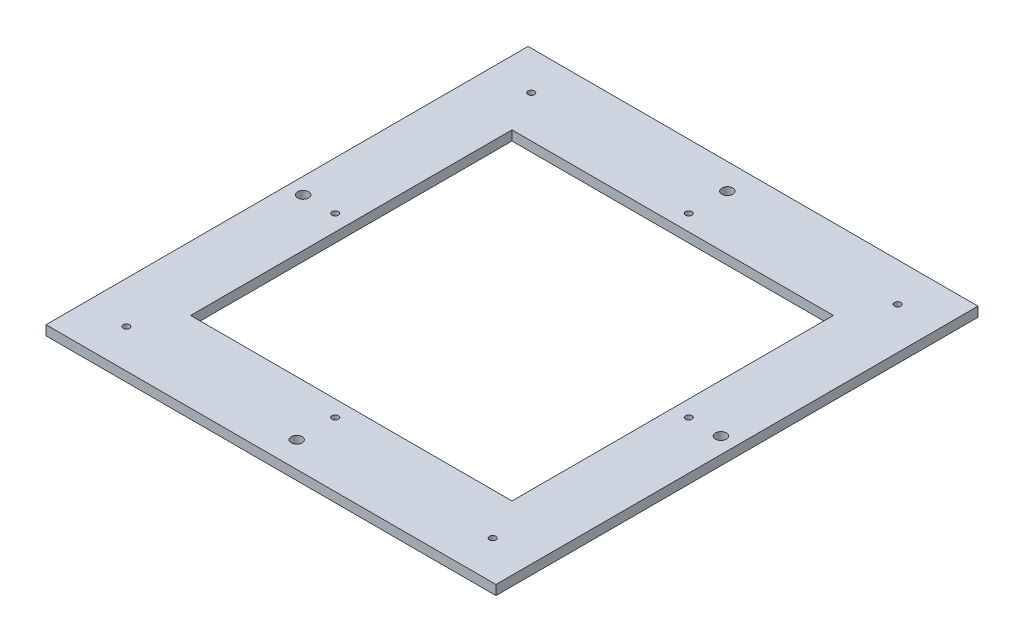
SolidWorks part; units mm, degrees
material "6061 合金"
ref_plane "前视基准面" through (0, 0, 0) normal (0, 0, 1) x (1, 0, 0)
ref_plane "上视基准面" through (0, 0, 0) normal (0, 1, 0) x (1, 0, 0)
ref_plane "右视基准面" through (0, 0, 0) normal (1, 0, 0) x (0, 0, -1)
sketch "草图1" plane through (0, 0, 0) normal (0, 0, 1) x (1, 0, 0)
  line L0 (12, 227.058) -> (152, 227.058)
  line L1 (12, 452.058) -> (12, 0) construction
  line L2 (152, 452.058) -> (152, 164.058) construction
  line L3 (152, 227.058) -> (12, 227.058) construction
extrude "拉伸-薄壁1" add sketch "草图1" along normal up to surface (150 mm away) thin contours L0
sketch "草图2" plane through (0, 224.058, 0) normal (0, -1, 0) x (1, 0, 0)
  line L1 (32, 125) -> (132, 125)
  line L2 (32, 125) -> (32, 25)
  line L3 (32, 25) -> (132, 25)
  line L4 (132, 125) -> (132, 25)
  line L5 (32, 125) -> (132, 25) construction
  line L6 (32, 25) -> (132, 125) construction
  point P0 (82, 75)
  point P2 (82, 75)
  dimension "D1" = 100
  dimension "D2" = 100
extrude "切除-拉伸1" cut sketch "草图2" against normal up to next
sketch "草图3" plane through (0, 224.058, 0) normal (0, -1, 0) x (1, 0, 0)
  line L3 (82, 75) -> (82, 142) construction
  line L10 (152, 150) -> (12, 150) construction
  line L11 (82, 75) -> (147, 75) construction
  line L12 (82, 75) -> (82, 8) construction
  line L13 (82, 75) -> (17, 75) construction
  line L14 (152, 150) -> (152, 0) construction
  line L15 (25, 150) -> (25, 0) construction
  line L16 (139, 150) -> (139, 0) construction
  line L17 (25, 150) -> (25, 0)
  line L18 (139, 150) -> (139, 0)
  line L27 (152, 150) -> (12, 150) construction
  line L28 (22, 135) -> (142, 135) construction
  line L29 (22, 135) -> (22, 15) construction
  line L30 (22, 15) -> (142, 15) construction
  line L31 (137, 20) -> (137, 130)
  line L32 (137, 130) -> (27, 130)
  line L33 (27, 130) -> (27, 20)
  line L34 (27, 20) -> (137, 20)
  line L35 (137, 20) -> (137, 130) construction
  line L36 (137, 130) -> (27, 130) construction
  line L37 (27, 130) -> (27, 20) construction
  line L38 (27, 20) -> (137, 20) construction
  line L39 (142, 135) -> (142, 15) construction
  line L40 (22, 135) -> (142, 15) construction
  line L41 (22, 15) -> (142, 135) construction
  line L42 (12, 0) -> (152, 0) construction
  point P1 (82, 20)
  point P7 (82, 130)
  point P11 (27, 75)
  point P12 (137, 75)
  point P22 (0, 0)
  point P23 (0, 0)
  point P24 (139, 12)
  point P25 (0, 0)
  point P26 (25, 12)
  point P30 (25, 138)
  point P34 (139, 138)
  point P40 (0, 0)
  point P41 (0, 0)
  point P42 (0, 0)
  point P43 (0, 0)
  point P44 (0, 0)
  point P49 (0, 0)
  point P52 (0, 0)
  point P53 (0, 0)
  point P54 (0, 0)
  point P55 (0, 0)
  point P56 (0, 0)
  point P57 (0, 0)
  point P58 (0, 0)
  point P59 (0, 0)
  point P60 (0, 0)
  point P61 (0, 0)
  point P62 (0, 0)
  point P63 (0, 0)
  point P64 (0, 0)
  point P65 (0, 0)
  point P66 (0, 0)
  point P67 (0, 0)
  dimension "D3" = 120
  dimension "D1" = 5
  dimension "D2" = 120
  dimension "D4" = 8
  dimension "D5" = 5
  dimension "D6" = 12
  dimension "D7" = 12
hole_wizard "M3 间隙孔1" positions "草图6" profile "草图7" hole size "M3" standard "GB" end condition through all
sketch "草图6" plane through (0, 224.058, 0) normal (0, -1, 0) x (-1, 0, 0)
  point P0 (-82, -142)
  point P3 (-147, -75)
  point P6 (-82, -8)
  point P9 (-17, -75)
sketch "草图7" plane through (82, 224.058, 142) normal (1, 0, 0) x (0, 0, -1)
  line L0 (0, 0) -> (0, 3)
  line L1 (0, 3) -> (1.7, 3)
  line L2 (1.7, 3) -> (1.7, 0)
  line L5 (1.7, 0) -> (0, 0)
  line L11 (0, -6.35) -> (0, 107.95) construction
  dimension "通孔孔直径" = 3.4
  dimension "通孔孔深度" = 3
hole_wizard "M3 螺纹孔的螺纹孔钻头1" positions "草图10" profile "草图11" hole size "M3" standard "GB" end condition through all
sketch "草图10" plane through (0, 224.058, 0) normal (0, -1, 0) x (-1, 0, 0)
  point P0 (-139, -138)
  point P3 (-25, -138)
  point P6 (-82, -130)
  point P9 (-27, -75)
  point P12 (-137, -75)
  point P15 (-82, -20)
  point P18 (-25, -12)
  point P21 (-139, -12)
sketch "草图11" plane through (139, 224.058, 138) normal (1, 0, 0) x (0, 0, -1)
  line L0 (0, 0) -> (0, 3)
  line L1 (0, 3) -> (1, 3)
  line L2 (1, 3) -> (1, 0)
  line L5 (1, 0) -> (0, 0)
  line L11 (0, -6.35) -> (0, 107.95) construction
  dimension "通孔孔直径" = 2
  dimension "通孔孔深度" = 3
equation "\"D2@草图2\"=\"D1@草图2\""
